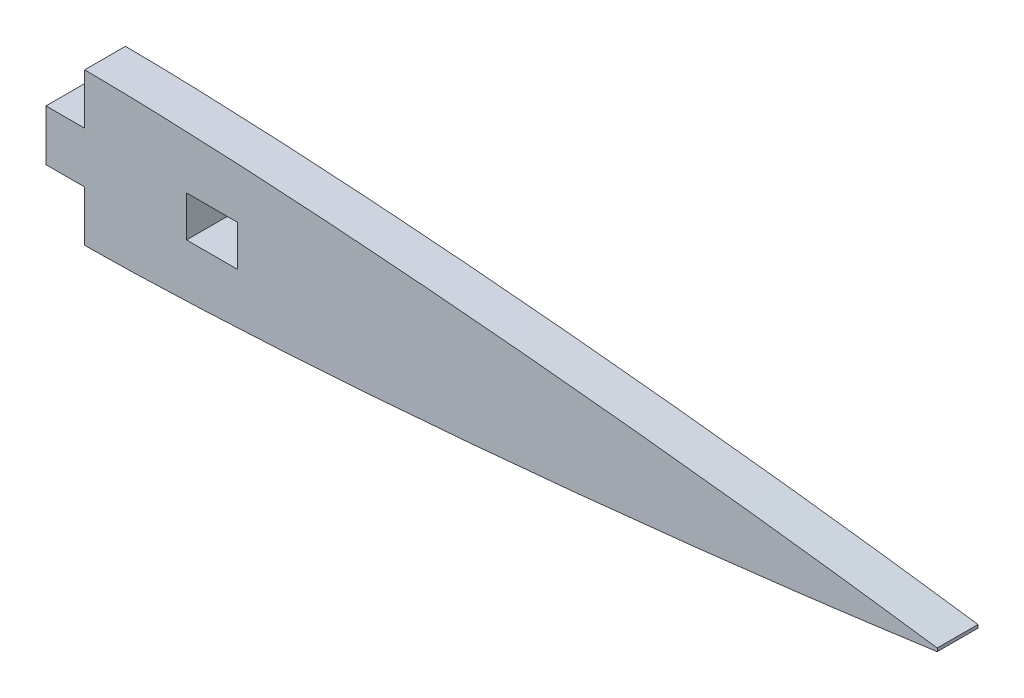
SolidWorks part; units mm, degrees
ref_plane "Front Plane" through (0, 0, 0) normal (0, 0, 1) x (1, 0, 0)
ref_plane "Top Plane" through (0, 0, 0) normal (0, 1, 0) x (1, 0, 0)
ref_plane "Right Plane" through (0, 0, 0) normal (1, 0, 0) x (0, 0, -1)
curve "Curve1"
  spline degree 3 poles (25.4, 0.032, 0) (24.9768, 0.0904, 0) (24.1307, 0.2071, 0) (22.8605, 0.3691, 0) (21.5905, 0.5229, 0) (20.3205, 0.6676, 0) (19.0504, 0.804, 0) (17.7804, 0.9321, 0) (16.5104, 1.0514, 0) (15.2404, 1.1606, 0) (13.9704, 1.2598, 0) (12.692, 1.3473, 0) (11.4135, 1.4221, 0) (10.1349, 1.4776, 0) (8.8649, 1.5185, 0) (7.8146, 1.5178, 0) (6.9766, 1.5373, 0) (6.35, 1.546, 0) (5.715, 1.5506, 0) (5.0799, 1.5478, 0) (4.4448, 1.5346, 0) (3.8095, 1.5078, 0) (3.1738, 1.462, 0) (2.5803, 1.3959, 0) (2.0289, 1.3055, 0) (1.6052, 1.2091, 0) (1.2675, 1.107, 0) (1.012, 1.0136, 0) (0.7549, 0.8965, 0) (0.4933, 0.743, 0) (0.2762, 0.5635, 0) (0.0851, 0.3233, 0) (-0.0556, 0, 0) (0.0851, -0.3233, 0) (0.2762, -0.5635, 0) (0.4933, -0.743, 0) (0.7549, -0.8965, 0) (1.012, -1.0136, 0) (1.2675, -1.107, 0) (1.6052, -1.2091, 0) (2.0289, -1.3055, 0) (2.5803, -1.3959, 0) (3.1738, -1.462, 0) (3.8095, -1.5078, 0) (4.4448, -1.5346, 0) (5.0799, -1.5478, 0) (5.715, -1.5506, 0) (6.35, -1.546, 0) (6.9766, -1.5373, 0) (7.8146, -1.5178, 0) (8.8649, -1.5185, 0) (10.1349, -1.4776, 0) (11.4135, -1.4221, 0) (12.692, -1.3473, 0) (13.9704, -1.2598, 0) (15.2404, -1.1606, 0) (16.5104, -1.0514, 0) (17.7804, -0.9321, 0) (19.0504, -0.804, 0) (20.3205, -0.6676, 0) (21.5905, -0.5229, 0) (22.8605, -0.3691, 0) (24.1307, -0.2071, 0) (24.9768, -0.0904, 0) (25.4, -0.032, 0) knots 0 0 0 0 0.024634 0.049243 0.07383 0.098397 0.122946 0.147479 0.171995 0.196494 0.220976 0.245442 0.27038 0.294813 0.319232 0.343642 0.35536 0.367566 0.379771 0.391975 0.404183 0.416399 0.428636 0.44092 0.450818 0.460843 0.465946 0.471149 0.476523 0.482208 0.488618 0.492568 0.5 0.507432 0.511382 0.517792 0.523477 0.528851 0.534054 0.539157 0.549182 0.55908 0.571364 0.583601 0.595817 0.608025 0.620229 0.632434 0.64464 0.656358 0.680768 0.705187 0.72962 0.754558 0.779024 0.803506 0.828005 0.852521 0.877054 0.901603 0.92617 0.950757 0.975366 1 1 1 1
sketch "Sketch2" plane through (0, 0, 0) normal (0, 0, 1) x (1, 0, 0)
  line L1 (158.75, -0.2) -> (158.75, 0.2)
  line L2 (47.625, -9.5258) -> (47.625, 9.5258)
  spline S1 degree 3 poles (158.75, 0.2) (156.1048, 0.5649) (150.8171, 1.2943) (142.8784, 2.3067) (134.9408, 3.2684) (127.0028, 4.1722) (119.0652, 5.0249) (111.1277, 5.8254) (103.1903, 6.5715) (95.2526, 7.254) (87.3152, 7.8739) (79.3248, 8.4206) (71.3345, 8.8884) (63.3434, 9.2348) (55.4583, 9.489) (50.2177, 9.4872) (47.625, 9.5258) knots 0 0 0 0 0.024634 0.049243 0.07383 0.098397 0.122946 0.147479 0.171995 0.196494 0.220976 0.245442 0.27038 0.294813 0.319232 0.343154 0.343154 0.343154 0.343154
  spline S2 degree 3 poles (47.625, -9.5258) (50.2177, -9.4872) (55.4583, -9.489) (63.3434, -9.2348) (71.3345, -8.8884) (79.3248, -8.4206) (87.3152, -7.8739) (95.2526, -7.254) (103.1903, -6.5715) (111.1277, -5.8254) (119.0652, -5.0249) (127.0028, -4.1722) (134.9408, -3.2684) (142.8784, -2.3067) (150.8171, -1.2943) (156.1048, -0.5649) (158.75, -0.2) knots 0.656846 0.656846 0.656846 0.656846 0.680768 0.705187 0.72962 0.754558 0.779024 0.803506 0.828005 0.852521 0.877054 0.901603 0.92617 0.950757 0.975366 1 1 1 1
  dimension "D1" = 47.625
extrude "Boss-Extrude1" add sketch "Sketch2" along normal blind 5.08
sketch "Sketch3" plane through (0, 0, 0) normal (0, 0, -1) x (-1, 0, 0)
  line L0 (-47.625, 9.5258) -> (-47.625, -9.5258) construction
  line L1 (-47.625, -9.5258) -> (-52.451, -9.5258)
  line L2 (-47.625, -9.5258) -> (-47.625, -3.175)
  line L3 (-47.625, -3.175) -> (-52.451, -3.175)
  line L4 (-52.451, -9.5258) -> (-52.451, -3.175)
  line L5 (-47.625, 3.175) -> (-52.451, 3.175)
  line L6 (-47.625, 3.175) -> (-47.625, 9.5258)
  line L7 (-47.625, 9.5258) -> (-52.451, 9.5258)
  line L8 (-52.451, 3.175) -> (-52.451, 9.5258)
  line L9 (-52.451, -3.175) -> (-52.451, 3.175) construction
  line L11 (-65.151, -2.54) -> (-71.501, -2.54)
  line L12 (-65.151, -2.54) -> (-65.151, 2.54)
  line L13 (-65.151, 2.54) -> (-71.501, 2.54)
  line L14 (-71.501, -2.54) -> (-71.501, 2.54)
  point P11 (-65.151, 0)
  point P13 (-52.451, 0)
  point P14 (-47.625, 0)
  dimension "D1" = 6.35
  dimension "D2" = 4.826
  dimension "D3" = 5.08
  dimension "D4" = 6.35
  dimension "D5" = 12.7
extrude "Cut-Extrude1" cut sketch "Sketch3" against normal through all
